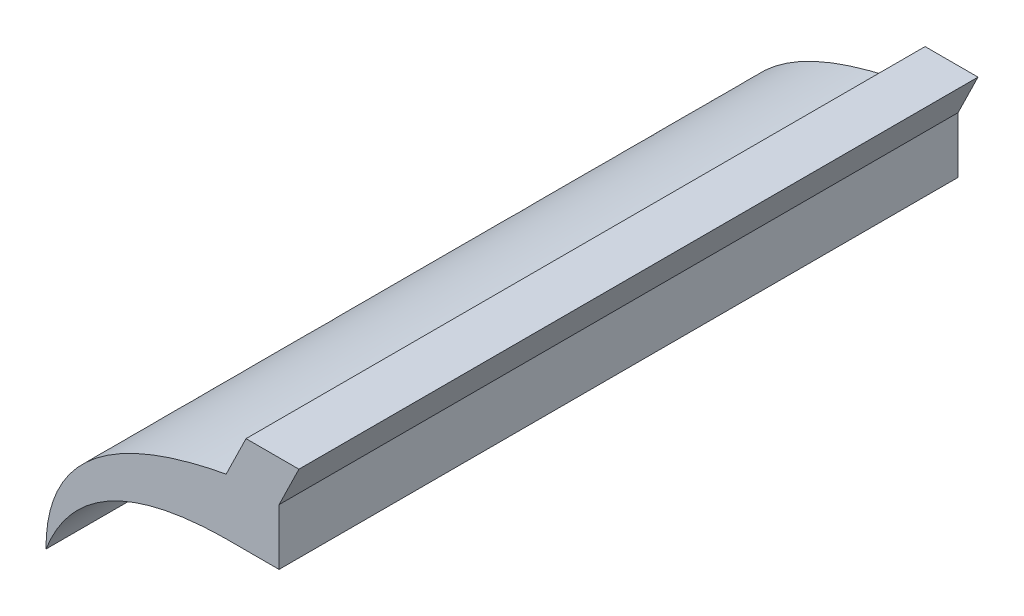
SolidWorks part; units mm, degrees
ref_plane "Front Plane" through (0, 0, 0) normal (0, 0, 1) x (1, 0, 0)
ref_plane "Top Plane" through (0, 0, 0) normal (0, 1, 0) x (1, 0, 0)
ref_plane "Right Plane" through (0, 0, 0) normal (1, 0, 0) x (0, 0, -1)
sketch "Sketch1" plane through (0, 0, 0) normal (0, 0, 1) x (1, 0, 0)
  line L0 (99.4402, 225.6228) -> (121.3832, 270.5505)
  line L1 (121.3832, 270.5505) -> (179.8133, 270.5505)
  line L2 (179.8133, 270.5505) -> (157.8702, 225.6228)
  line L3 (-99.4402, 54.4112) -> (-99.5275, 54.4599)
  line L4 (99.4402, 225.6228) -> (157.8702, 225.6228)
  line L5 (157.8702, 225.6228) -> (157.8702, 163.6734)
  line L6 (157.8702, 163.6734) -> (99.4402, 163.6734)
  line L7 (99.4402, 225.6228) -> (99.4402, 163.6734)
  line L8 (99.4402, 225.6228) -> (157.8702, 225.6228)
  spline S0 degree 2 poles (-99.5275, 54.4599) (-58.241, 162.2) (99.4402, 163.6734) knots 0 0 0 1 1 1
  spline S1 degree 2 poles (-99.5275, 54.4599) (-100.3318, 188.2944) (99.4402, 225.6228) knots 0 0 0 1 1 1
  dimension "D1" = 50
extrude "Boss-Extrude1" add sketch "Sketch1" along normal blind 750 contours S1 S0 L7 | L4 L7 L6 L5 | L0 L4 L2 L1
